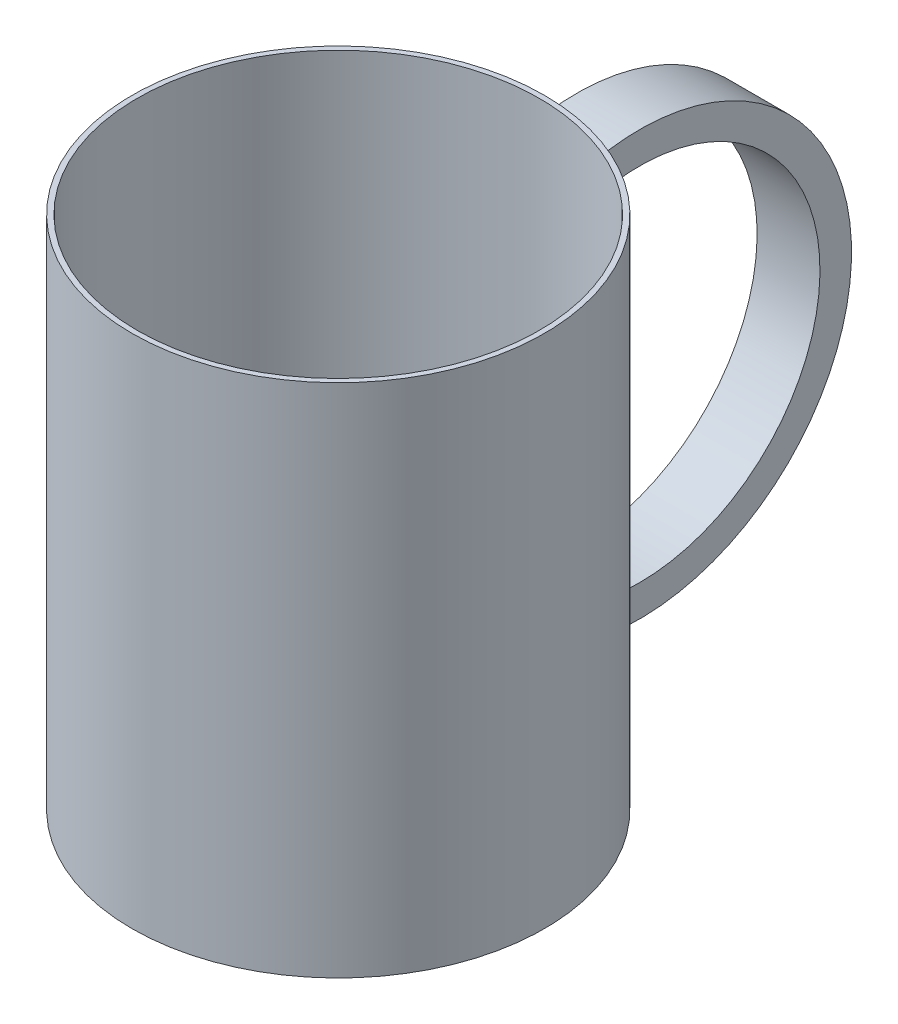
SolidWorks part; units mm, degrees
ref_plane "Front Plane" through (0, 0, 0) normal (0, 0, 1) x (1, 0, 0)
ref_plane "Top Plane" through (0, 0, 0) normal (0, 1, 0) x (1, 0, 0)
ref_plane "Right Plane" through (0, 0, 0) normal (1, 0, 0) x (0, 0, -1)
sketch "Sketch3" plane through (0, 0, 0) normal (1, 0, 0) x (0, 0, -1)
  line L0 (0, -50) -> (0, 50)
  line L1 (0, 55) -> (0, -55) construction
  line L3 (0, 50) -> (40, 50)
  line L4 (40, 50) -> (40, -50)
  line L5 (40, -50) -> (0, -50)
  point P6 (0, 0)
  dimension "D1" = 40
  dimension "D2" = 100
revolve "Revolve2" add sketch "Sketch3" angle 360 about L0
sketch "Sketch6" plane through (0, 0, 0) normal (1, 0, 0) x (0, 0, -1)
  line L0 (40, -50) -> (40, 50) construction
  line L1 (40, -50) -> (40, 50) construction
  arc A0 (40, 36) -> (40, -36) centre (52.345, 0) cw
  circle A1 centre (52.345, 0) radius 38.0578
  point P11 (52.345, 0)
  dimension "D1" = 14
  dimension "D2" = 14
ref_plane "Plane5" through (0, 36, -40) normal (0, 0.3244, -0.9459) x (-1, 0, 0)
sketch "Sketch8" plane through (0, 36, -40) normal (0, 0.3244, -0.9459) x (-1, 0, 0)
  line L1 (-6.0982, 3.0587) -> (6.0982, 3.0587)
  line L2 (-6.0982, 3.0587) -> (-6.0982, -3.0587)
  line L3 (-6.0982, -3.0587) -> (6.0982, -3.0587)
  line L4 (6.0982, 3.0587) -> (6.0982, -3.0587)
  line L5 (-6.0982, 3.0587) -> (6.0982, -3.0587) construction
  line L6 (-6.0982, -3.0587) -> (6.0982, 3.0587) construction
  point P0 (0, 0)
sketch "Sketch9" plane through (0, 36, -40) normal (0, 0.3244, -0.9459) x (-1, 0, 0)
  line L1 (-4.1018, 1.65) -> (4.1018, 1.65)
  line L2 (-4.1018, 1.65) -> (-4.1018, -1.65)
  line L3 (-4.1018, -1.65) -> (4.1018, -1.65)
  line L4 (4.1018, 1.65) -> (4.1018, -1.65)
  line L5 (-4.1018, 1.65) -> (4.1018, -1.65) construction
  line L6 (-4.1018, -1.65) -> (4.1018, 1.65) construction
  point P0 (0, 0)
sweep "Sweep1" add profiles "Sketch8" path "Sketch6"
sketch "Sketch10" plane through (0, 0, 0) normal (0, 1, 0) x (1, 0, 0)
  circle A0 centre (0, 0) radius 39
  dimension "D1" = 78
extrude "Cut-Extrude1" cut sketch "Sketch10" against normal blind 40 and the other way blind 50
